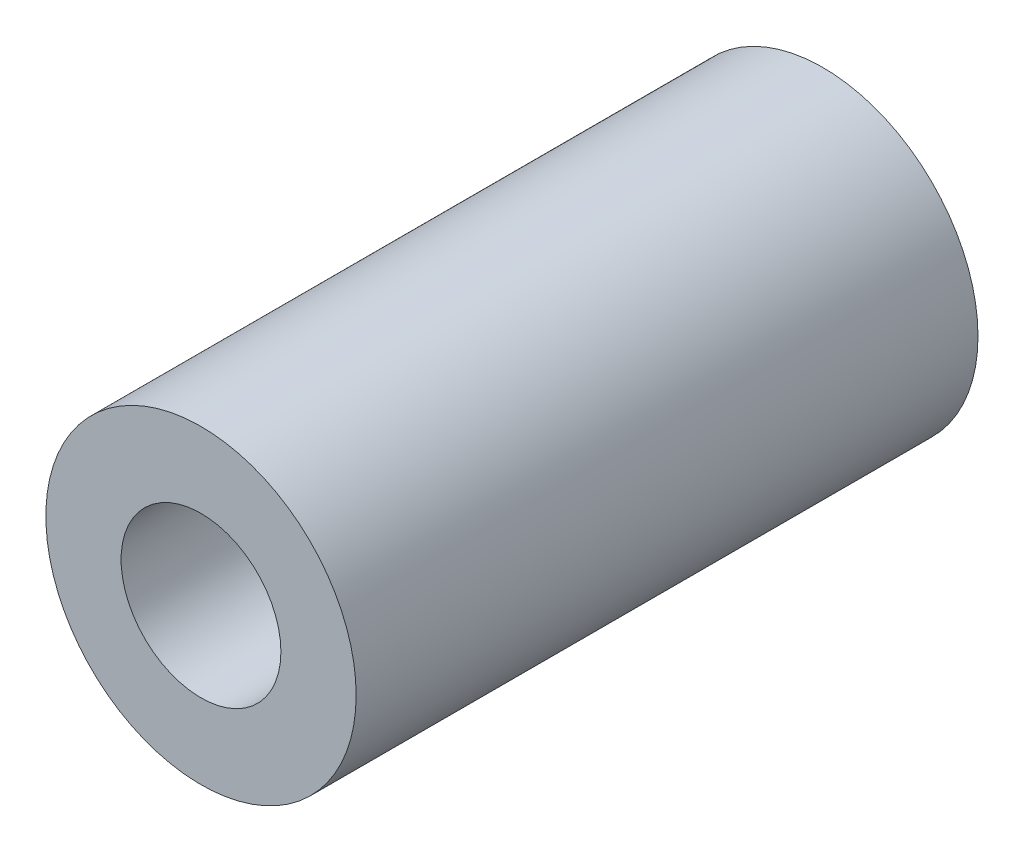
SolidWorks part; units mm, degrees
material "Nylon 6/10"
ref_plane "Front Plane" through (0, 0, 0) normal (0, 0, 1) x (1, 0, 0)
ref_plane "Top Plane" through (0, 0, 0) normal (0, 1, 0) x (1, 0, 0)
ref_plane "Right Plane" through (0, 0, 0) normal (1, 0, 0) x (0, 0, -1)
sketch "Sketch1" plane through (0, 0, 0) normal (0, 0, 1) x (1, 0, 0)
  circle A0 centre (59.1947, -18.4067) radius 3.2639
  circle A1 centre (59.1947, -18.4067) radius 6.3373
  dimension "D1" = 6.5278
extrude "Boss-Extrude1" add sketch "Sketch1" along normal up to surface (25.4 mm away)
